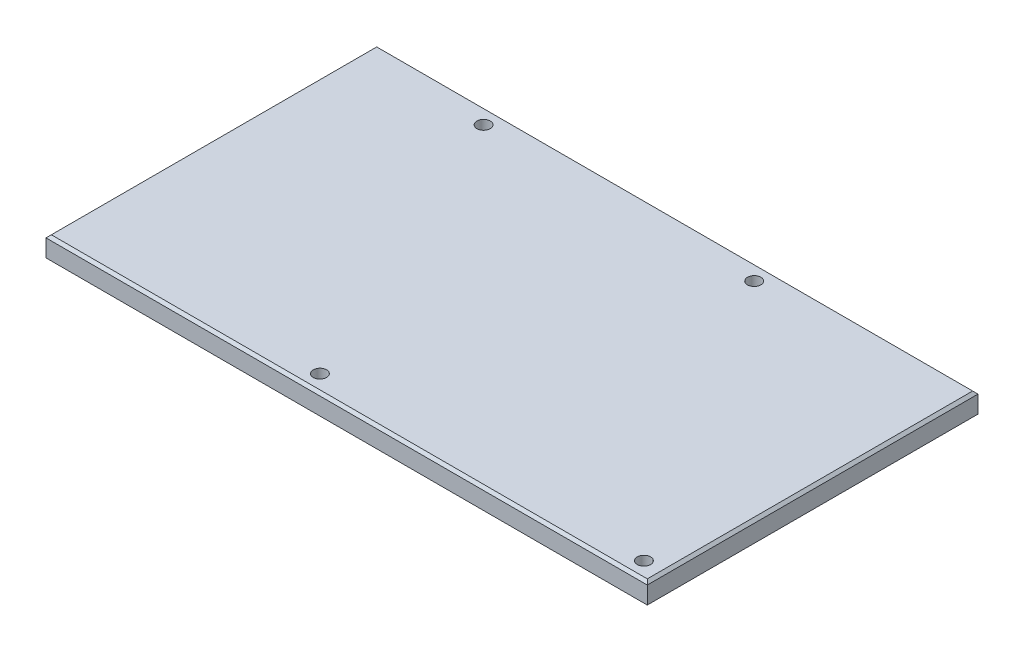
SolidWorks part; units mm, degrees
ref_plane "Front Plane" through (0, 0, 0) normal (0, 0, 1) x (1, 0, 0)
ref_plane "Top Plane" through (0, 0, 0) normal (0, 1, 0) x (1, 0, 0)
ref_plane "Right Plane" through (0, 0, 0) normal (1, 0, 0) x (0, 0, -1)
sketch "Sketch1" plane through (0, 0, 0) normal (0, 1, 0) x (1, 0, 0)
  line L1 (-62.8448, 34.9914) -> (117.1552, 34.9914)
  line L2 (-62.8448, 34.9914) -> (-62.8448, -64.0086)
  line L3 (-62.8448, -64.0086) -> (117.1552, -64.0086)
  line L4 (117.1552, 34.9914) -> (117.1552, -64.0086)
  dimension "D1" = 180
  dimension "D2" = 99
extrude "Boss-Extrude1" add sketch "Sketch1" along normal blind 6
hole_wizard "Ø4.0 (4) Diameter Hole1" positions "Sketch2" profile "Sketch4" hole size "Ø4.0" standard "DIN" end condition through all
sketch "Sketch2" plane through (0, 6, 0) normal (0, 1, 0) x (1, 0, 0)
  line L0 (117.1552, -64.0086) -> (117.1552, 34.9914) construction
  line L1 (-62.8448, -64.0086) -> (117.1552, -64.0086) construction
  point P0 (111.1552, -59.0086)
  dimension "D1" = 6
  dimension "D2" = 5
sketch "Sketch4" plane through (111.1552, 6, 59.0086) normal (1, 0, 0) x (0, 0, 1)
  line L0 (0, 0) -> (0, 6)
  line L1 (0, 6) -> (2, 6)
  line L2 (2, 6) -> (2, 0)
  line L5 (2, 0) -> (0, 0)
  line L11 (0, -6.35) -> (0, 107.95) construction
  dimension "Thru Hole Dia." = 4
  dimension "Thru Hole Depth" = 6
hole_wizard "Ø4.0 (4) Diameter Hole2" positions "Sketch5" profile "Sketch6" hole size "Ø4.0" standard "DIN" end condition through all
sketch "Sketch5" plane through (0, 6, 0) normal (0, 1, 0) x (1, 0, 0)
  line L0 (117.1552, -64.0086) -> (117.1552, 34.9914) construction
  line L1 (117.1552, 34.9914) -> (-62.8448, 34.9914) construction
  point P0 (55.1552, 29.9914)
  dimension "D1" = 62
  dimension "D2" = 5
sketch "Sketch6" plane through (55.1552, 6, -29.9914) normal (1, 0, 0) x (0, 0, 1)
  line L0 (0, 0) -> (0, 6)
  line L1 (0, 6) -> (2, 6)
  line L2 (2, 6) -> (2, 0)
  line L5 (2, 0) -> (0, 0)
  line L11 (0, -6.35) -> (0, 107.95) construction
  dimension "Thru Hole Dia." = 4
  dimension "Thru Hole Depth" = 6
pattern_linear "LPattern1" count 2 spacing 97 along (-1, 0, 0) of "Ø4.0 (4) Diameter Hole1"
pattern_linear "LPattern2" count 2 spacing 81 along (-1, 0, 0) of "Ø4.0 (4) Diameter Hole2"
chamfer "Chamfer1" distance 0.8 angle 45 4 edges at (-62.8448, 6, 14.5086) (27.1552, 6, -34.9914) (117.1552, 6, 14.5086) (27.1552, 6, 64.0086)
